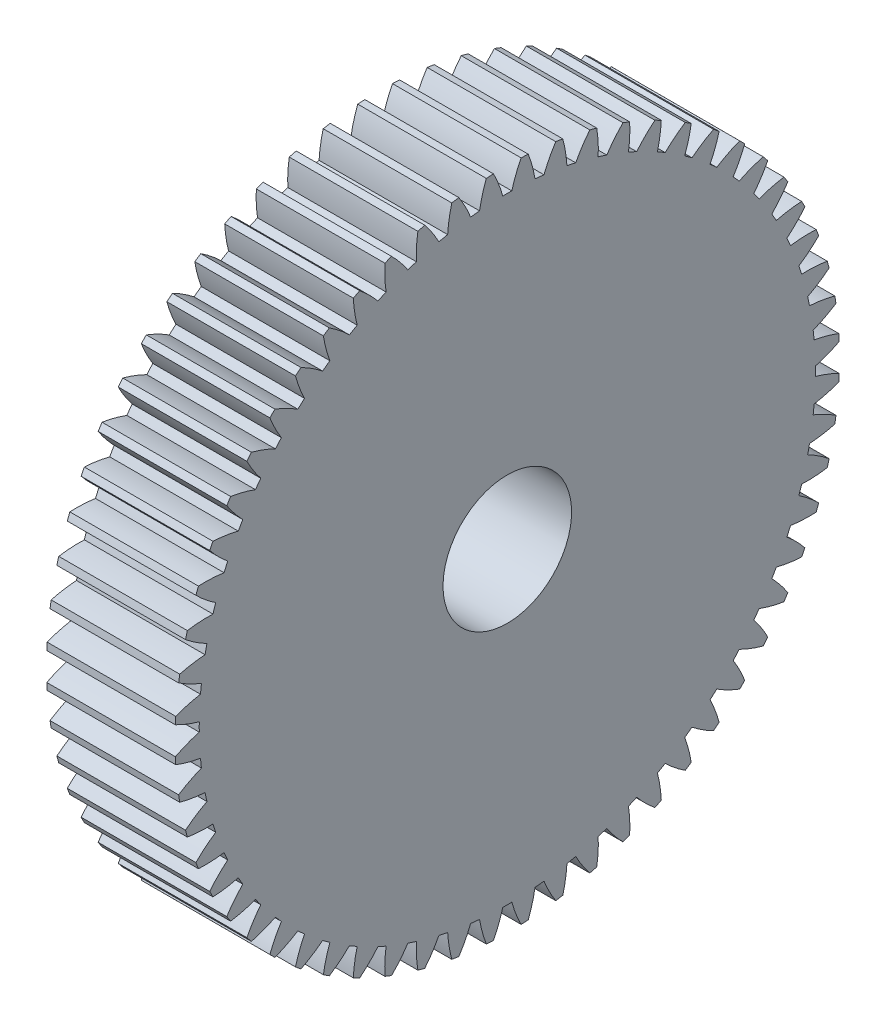
SolidWorks part; units mm, degrees
ref_plane "Plane1" through (0, 0, 0) normal (0, 0, 1) x (1, 0, 0)
ref_plane "Plane2" through (0, 0, 0) normal (0, 1, 0) x (1, 0, 0)
ref_plane "Plane3" through (0, 0, 0) normal (1, 0, 0) x (0, 0, -1)
sketch "HoldingSke" plane through (0, 0, 0) normal (0, 1, 0) x (1, 0, 0)
  line L0 (0, 0) -> (2, -3.4641)
  line L1 (-15, 0) -> (100, 0) construction
  line L2 (0, 0) -> (-2.1039, 2.3779)
  line L3 (0, 0) -> (-11.863, 4.5341)
  line L4 (0, 0) -> (4.318, 7.479)
  line L5 (0, 0) -> (-46.8476, -17.4728)
  line L6 (0, 0) -> (-2.4869, -1.6779)
  line L7 (-2.1039, 2.3779) -> (8.6586, 51.2059)
  line L8 (-76.2, 54.61) -> (-75.7, 54.61)
  line L9 (-71.009, 38.7566) -> (-53.1078, 45.2721)
  line L10 (-76.2, 71.12) -> (104.1128, 71.12)
  line L11 (0, 0) -> (-3, 0)
  line L12 (-76.2, 101.6) -> (-76.192, 101.6)
  line L13 (24.9733, 27.94) -> (52.9518, 28.4284)
  line L14 (24.9733, 27.94) -> (24.9743, 27.94)
  line L15 (24.9733, 27.94) -> (100.4006, 29.5858)
  line L16 (-63.627, -0.25) -> (-12.827, -0.25)
  circle A0 centre (0, 0) radius 1.5
  circle A1 centre (0, 0) radius 7.1865
  circle A2 centre (0, 0) radius 37.5
  circle A3 centre (0, 0) radius 1.5
  dimension "MHD" = 14.373
  dimension "Hub_dia" = 75
  dimension "Bore" = 3
  dimension "MBD" = 3
  dimension "Num_teeth" = 60
  dimension "Pitch" = 4
  dimension "Overall_len" = 50
  dimension "Show_teeth" = 60
  dimension "Thickness" = 3
  dimension "OAL" = 50.0001
  dimension "T_dim" = 0.5
  dimension "Ap" = 20
  dimension "H" = 19.05
  dimension "Pitch_radius" = 180.3128
  dimension "Width" = 3
  dimension "Backlash" = 0.008
  dimension "Addendum_fac" = 1
  dimension "Dedendum_fac" = 1.25
  dimension "Clearance_fac" = 0.25
  dimension "Dedendum_add" = 0.001
  dimension "Module" = 0.25
sketch "BasProSke" plane through (0, 0, 0) normal (0, 1, 0) x (1, 0, 0)
  line L0 (-10, 0) -> (60, 0) construction
  line L1 (0, 0) -> (0, 7.75)
  line L2 (0, 0) -> (3, 0)
  line L3 (3, 0) -> (3, 7.75)
  line L4 (3, 7.75) -> (0, 7.75)
  dimension "Thickness" = 3
  dimension "Diameter" = 15.5
revolve "Base-Revolve" add sketch "BasProSke" angle 360 about L0
sketch "TooCutSke" plane through (0, 0, 0) normal (1, 0, 0) x (0, 0, -1)
  line L1 (0, 0) -> (0, 107) construction
  line L2 (0, 0) -> (-0.2103, 7.4971) construction
  line L3 (0, 0) -> (-0.7848, 14.975) construction
  line L4 (-0.2103, 7.4971) -> (-0.3924, 7.4875) construction
  arc A0 (0.1048, 7.1857) -> (-0.1048, 7.1857) centre (0, 0) ccw
  arc A1 (0.3351, 7.7682) -> (-0.3351, 7.7682) centre (0, 0) ccw
  circle A2 centre (0, 0) radius 7.5 construction
  circle A3 centre (0, 0) radius 7.0477 construction
  arc A4 (-0.1048, 7.1857) -> (-0.3351, 7.7682) centre (-2.9945, 6.3799) ccw
  arc A5 (0.3351, 7.7682) -> (0.1048, 7.1857) centre (2.9945, 6.3799) ccw
  dimension "Root_dia" = 14.373
  dimension "Overcut_dia" = 15.5508
  dimension "Pitch_dia" = 15
  dimension "Base_dia" = 14.0954
  dimension "Flank_rad" = 3
  dimension "Half_ang" = 3
  dimension "Half_CT" = 0.1823
extrude "ToothCut" cut sketch "TooCutSke" along normal through all
fillet "Breaks" [suppressed] radius 0.005
fillet "RootFillets" [suppressed] radius 0.0635
pattern_circular "TeethCuts" count 60 every 6 about axis through (-10, 0, 0) along (1, 0, 0) of "ToothCut", "RootFillets", "Breaks"
sketch "HubNeaOneSke" plane through (0, 0, 0) normal (-1, 0, 0) x (0, 0, 1)
  circle A0 centre (0, 0) radius 7.1865
  dimension "Diameter" = 14.373
extrude "HubNearOne" [suppressed] add sketch "HubNeaOneSke" along normal blind 47.0001
sketch "HubNeaBotSke" plane through (0, 0, 0) normal (-1, 0, 0) x (0, 0, 1)
  circle A0 centre (0, 0) radius 7.1865
  dimension "Diameter" = 14.373
extrude "HubNearBoth" [suppressed] add sketch "HubNeaBotSke" along normal blind 23.5
ref_plane "FarPln" through (3, 0, 0) normal (1, 0, 0) x (0, 0, -1)
sketch "HubFarSke" plane through (3, 0, 0) normal (1, 0, 0) x (0, 0, -1)
  circle A0 centre (0, 0) radius 7.1865
  dimension "Diameter" = 14.373
extrude "HubFar" [suppressed] add sketch "HubFarSke" along normal blind 23.5
sketch "BorSke" plane through (0, 0, 0) normal (1, 0, 0) x (0, 0, -1)
  circle A0 centre (0, 0) radius 1.5
  dimension "Diameter" = 3
extrude "Bore" cut sketch "BorSke" along normal mid plane 100.0001
sketch "KeySke" plane through (0, 0, 0) normal (1, 0, 0) x (0, 0, -1)
  line L0 (-0.6, 0) -> (-0.6, 2)
  line L1 (-0.6, 2) -> (0.6, 2)
  line L2 (0.6, 2) -> (0.6, 0)
  line L3 (0, 0) -> (0, 34) construction
  line L4 (-0.6, 0) -> (0.6, 0)
  dimension "Offset" = 2
  dimension "Width" = 1.2
extrude "Keyway" [suppressed] cut sketch "KeySke" along normal mid plane 100.0001
pattern_circular "Keyway2" [suppressed] count 2 every 90 about axis through (-10, 0, 0) along (1, 0, 0)
equation "' \"Module@HoldingSke\" = 6.35"
equation "' \"Num_teeth@HoldingSke\" = 12"
equation "' \"Ap@HoldingSke\" =  20"
equation "' \"Ap@HoldingSke\" = 20"
equation "' \"Width@HoldingSke\" = 0.5 * 25.4"
equation "' \"Hub_dia@HoldingSke\"= 1 * 25.4"
equation "' \"Hub_dia@HoldingSke\" = 1 * 25.4"
equation "' \"Overall_len@HoldingSke\" = 1.0 * 25.4"
equation "' \"Bore@HoldingSke\" = 0.75 * 25.4"
equation "' \"T_dim@HoldingSke\" = 0.1 * 25.4"
equation "' \"Width@KeySke\" = 0.25 * 25.4"
equation "' \"Show_teeth@HoldingSke\" = 13"
equation "' \"Backlash@HoldingSke\" = 0.009 * 25.4"
equation "' \"Addendum_fac@HoldingSke\" = 1.0"
equation "' \"Dedendum_fac@HoldingSke\" = 1.25"
equation "' \"Dedendum_add@HoldingSke\" = 0.00005 * 25.4"
equation "' \"Clearance_fac@HoldingSke\" = 0.25"
equation "\"Pitch@HoldingSke\" = 1 / \"Module@HoldingSke\""
equation "\"Overcut_dia@TooCutSke\" = (\"Num_teeth@HoldingSke\" + 2 * \"Addendum_fac@HoldingSke\") / \"Pitch@HoldingSke\" + 0.002 * 25.4"
equation "\"Pitch_dia@TooCutSke\" = \"Num_teeth@HoldingSke\" / \"Pitch@HoldingSke\""
equation "\"Base_dia@TooCutSke\" = \"Num_teeth@HoldingSke\" / \"Pitch@HoldingSke\" * cos((\"Ap@HoldingSke\"  * 3.14159265 / 180))"
equation "\"Root_dia@TooCutSke\" = (\"Num_teeth@HoldingSke\" + 2) / \"Pitch@HoldingSke\" - 2 * (\"Addendum_fac@HoldingSke\" + \"Dedendum_fac@HoldingSke\") / \"Pitch@HoldingSke\" - \"Dedendum_add@HoldingSke\" * 2"
equation "\"Half_ang@TooCutSke\" = 180 / \"Num_teeth@HoldingSke\""
equation "\"Half_CT@TooCutSke\" = \"Num_teeth@HoldingSke\" / \"Pitch@HoldingSke\" * sin((3.14159265 / 2 / \"Num_teeth@HoldingSke\")) / 2 - 7 * \"Backlash@HoldingSke\" / 4"
equation "\"Flank_rad@TooCutSke\" = \"Num_teeth@HoldingSke\" / \"Pitch@HoldingSke\" / 5"
equation "\"Radius@RootFillets\" = \"Clearance_fac@HoldingSke\" / \"Pitch@HoldingSke\" + \"Dedendum_add@HoldingSke\""
equation "\"Break_rad@Breaks\" = 0.02 / \"Pitch@HoldingSke\""
equation "\"Thickness@HoldingSke\" = \"Width@HoldingSke\""
equation "\"OAL@HoldingSke\" = \"Thickness@HoldingSke\""
equation "\"MHD@HoldingSke\" = (\"Num_teeth@HoldingSke\" + 2) / \"Pitch@HoldingSke\" - 2 * (\"Addendum_fac@HoldingSke\" + \"Dedendum_fac@HoldingSke\")  / \"Pitch@HoldingSke\" - \"Dedendum_add@HoldingSke\" * 2"
equation "\"MBD@HoldingSke\" = (\"Num_teeth@HoldingSke\" + 2) / \"Pitch@HoldingSke\" - 2 * (\"Addendum_fac@HoldingSke\" + \"Dedendum_fac@HoldingSke\")  / \"Pitch@HoldingSke\" - \"Dedendum_add@HoldingSke\" * 2 - 0.002 * 25.4"
equation "\"MHD@HoldingSke\" = ((sgn( \"MHD@HoldingSke\" - \"Hub_dia@HoldingSke\" )-1)*( \"MHD@HoldingSke\" - \"Hub_dia@HoldingSke\" ))/-2+ \"Hub_dia@HoldingSke\""
equation "\"MBD@HoldingSke\" = ((sgn( \"MBD@HoldingSke\" - \"Bore@HoldingSke\" )-1)*( \"MBD@HoldingSke\" - \"Bore@HoldingSke\" ))/-2+ \"Bore@HoldingSke\""
equation "\"OAL@HoldingSke\" = ((sgn( \"OAL@HoldingSke\" - \"Overall_len@HoldingSke\" )+1)*( \"OAL@HoldingSke\" - \"Overall_len@HoldingSke\" ))/2 + \"Overall_len@HoldingSke\" + 0.000002 * 25.4"
equation "\"Num_teeth@TeethCuts\" = int( \"Show_teeth@HoldingSke\" ) + 1"
equation "\"Num_teeth@TeethCuts\" = ((sgn( \"Num_teeth@TeethCuts\" - \"Num_teeth@HoldingSke\" )-1)*( \"Num_teeth@TeethCuts\" - \"Num_teeth@HoldingSke\" ))/-2+ \"Num_teeth@HoldingSke\""
equation "\"Num_teeth@TeethCuts\" = ((sgn( \"Num_teeth@TeethCuts\" - 2.0)+1)*( \"Num_teeth@TeethCuts\" - 2.0))/2 +2.0"
equation "\"Angle@TeethCuts\" = 360.0 / \"Num_teeth@HoldingSke\""
equation "\"Diameter@BasProSke\" = (\"Num_teeth@HoldingSke\" + 2 * \"Addendum_fac@HoldingSke\") / \"Pitch@HoldingSke\""
equation "\"Thickness@BasProSke\"  = \"Thickness@HoldingSke\""
equation "' \"Fillet_rad@BasProSke\" =  \"Thickness@HoldingSke\" * 0.05"
equation "' \"Fillet_rad@BasProSke\" = \"Thickness@HoldingSke\" * 0.05"
equation "\"MHD@HoldingSke\" = ((sgn( \"MHD@HoldingSke\" - \"Root_dia@TooCutSke\" )-1)*( \"MHD@HoldingSke\" - \"Root_dia@TooCutSke\" ))/-2+ \"Root_dia@TooCutSke\""
equation "\"Diameter@HubNeaOneSke\" = \"MHD@HoldingSke\""
equation "\"Length@HubNearOne\" = \"OAL@HoldingSke\" - \"Thickness@BasProSke\""
equation "\"Diameter@HubNeaBotSke\" = \"MHD@HoldingSke\""
equation "\"Length@HubNearBoth\" = ( \"OAL@HoldingSke\" - \"Thickness@BasProSke\" ) / 2.0"
equation "\"Thickness@FarPln\" = \"Thickness@BasProSke\""
equation "\"Diameter@HubFarSke\" = \"MHD@HoldingSke\""
equation "\"Length@HubFar\" = ( \"OAL@HoldingSke\" - \"Thickness@BasProSke\" ) / 2.0"
equation "\"Diameter@BorSke\" = \"MBD@HoldingSke\""
equation "\"D1@Bore\" = \"OAL@HoldingSke\" * 2.0"
equation "\"D1@Keyway\" = \"OAL@HoldingSke\" * 2.0"
equation "\"Offset@KeySke\" = \"T_dim@HoldingSke\" + \"MBD@HoldingSke\" / 2.0"
